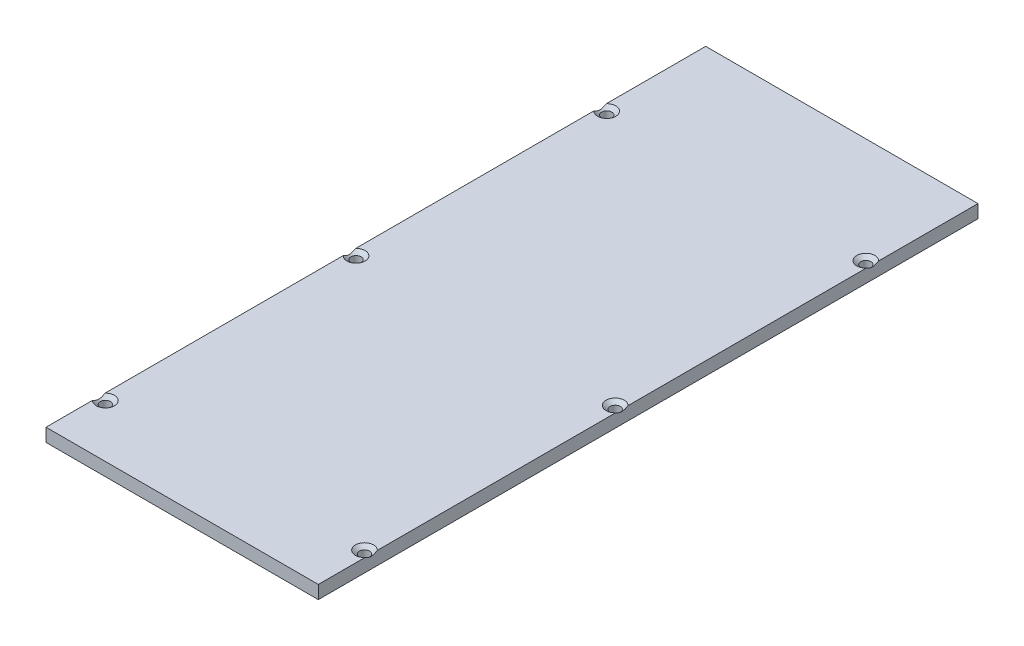
SolidWorks part; units mm, degrees
material "Delrin"
ref_plane "Front Plane" through (0, 0, 0) normal (0, 0, 1) x (1, 0, 0)
ref_plane "Top Plane" through (0, 0, 0) normal (0, 1, 0) x (1, 0, 0)
ref_plane "Right Plane" through (0, 0, 0) normal (1, 0, 0) x (0, 0, -1)
sketch "Sketch1" plane through (0, 0, 0) normal (0, 1, 0) x (1, 0, 0)
  line L1 (-32.766, 79.375) -> (32.766, 79.375)
  line L2 (-32.766, 79.375) -> (-32.766, -79.375)
  line L3 (-32.766, -79.375) -> (32.766, -79.375)
  line L4 (32.766, 79.375) -> (32.766, -79.375)
  dimension "D1" = 158.75
  dimension "D2" = 79.375
  dimension "D3" = 32.766
  dimension "D4" = 65.532
extrude "Extrude1" add sketch "Sketch1" along normal blind 3.175
hole_wizard "CSK for #2 Flat Head Machine Screw (100)1" positions "3DSketch1" profile "Sketch2" countersink size "#2" standard "Ansi Inch" end condition through all
sketch3d "3DSketch1"
  line L11 (32.766, 3.175, -79.375) -> (-32.766, 3.175, -79.375) construction
  line L12 (-32.766, 3.175, -79.375) -> (-32.766, 3.175, 79.375) construction
  line L13 (32.766, 3.175, 79.375) -> (32.766, 3.175, -79.375) construction
  line L14 (-32.766, 3.175, 79.375) -> (32.766, 3.175, 79.375) construction
  point P42 (-31.1785, 3.175, -53.975)
  point P44 (-31.1785, 3.175, 66.675)
  point P46 (-31.1785, 3.175, 6.35)
  point P48 (31.1785, 3.175, -53.975)
  point P50 (31.1785, 3.175, 6.35)
  point P52 (31.1785, 3.175, 66.675)
  dimension "D4" = 1.5875
  dimension "D5" = 1.5875
  dimension "D6" = 12.7
  dimension "D7" = 85.725
  dimension "D8" = 25.4
sketch "Sketch2" plane through (-31.1785, 3.175, -53.975) normal (1, 0, 0) x (0, 0, 1)
  line L0 (0, 0) -> (0, 3.175)
  line L1 (0, 3.175) -> (1.2192, 3.175)
  line L2 (1.2192, 3.175) -> (1.2192, 0.8099)
  line L3 (1.2192, 0.8099) -> (2.1844, 0)
  line L5 (2.1844, 0) -> (0, 0)
  line L6 (-1.2192, 0.8099) -> (-2.1844, 0) construction
  line L11 (0, -6.35) -> (0, 107.95) construction
  dimension "Thru Hole Dia." = 2.4384
  dimension "Thru Hole Depth" = 3.175
  dimension "Near C'Sink Dia." = 4.3688
  dimension "Near C'Sink Angle" = 100
hole_wizard "Tap Drill for #2 Tap1" positions "3DSketch2" profile "Sketch3" hole size "#2-56" standard "Ansi Inch"
sketch3d "3DSketch2"
  line L0 (32.766, 3.175, -79.375) -> (32.766, 0, -79.375) construction
  line L1 (-32.766, 3.175, -79.375) -> (-32.766, 0, -79.375) construction
  line L2 (32.766, 0, -79.375) -> (-32.766, 0, -79.375) construction
  point P0 (-26.416, 1.5875, -79.375)
  point P2 (26.416, 1.5875, -79.375)
  dimension "D1" = 6.35
  dimension "D2" = 6.35
  dimension "D3" = 1.5875
  dimension "D4" = 1.5875
sketch "Sketch3" plane through (-26.416, 1.5875, -79.375) normal (1, 0, 0) x (0, 1, 0)
  line L0 (0, 0) -> (0, 6.8842)
  line L1 (0, 6.8842) -> (0.889, 6.35)
  line L2 (0.889, 6.35) -> (0.889, 0)
  line L5 (0.889, 0) -> (0, 0)
  line L10 (0, 6.8842) -> (-0.889, 6.35) construction
  line L11 (0, -6.35) -> (0, 107.95) construction
  dimension "Hole Dia." = 1.778
  dimension "Hole Depth" = 6.35
  dimension "Drill Angle" = 118
